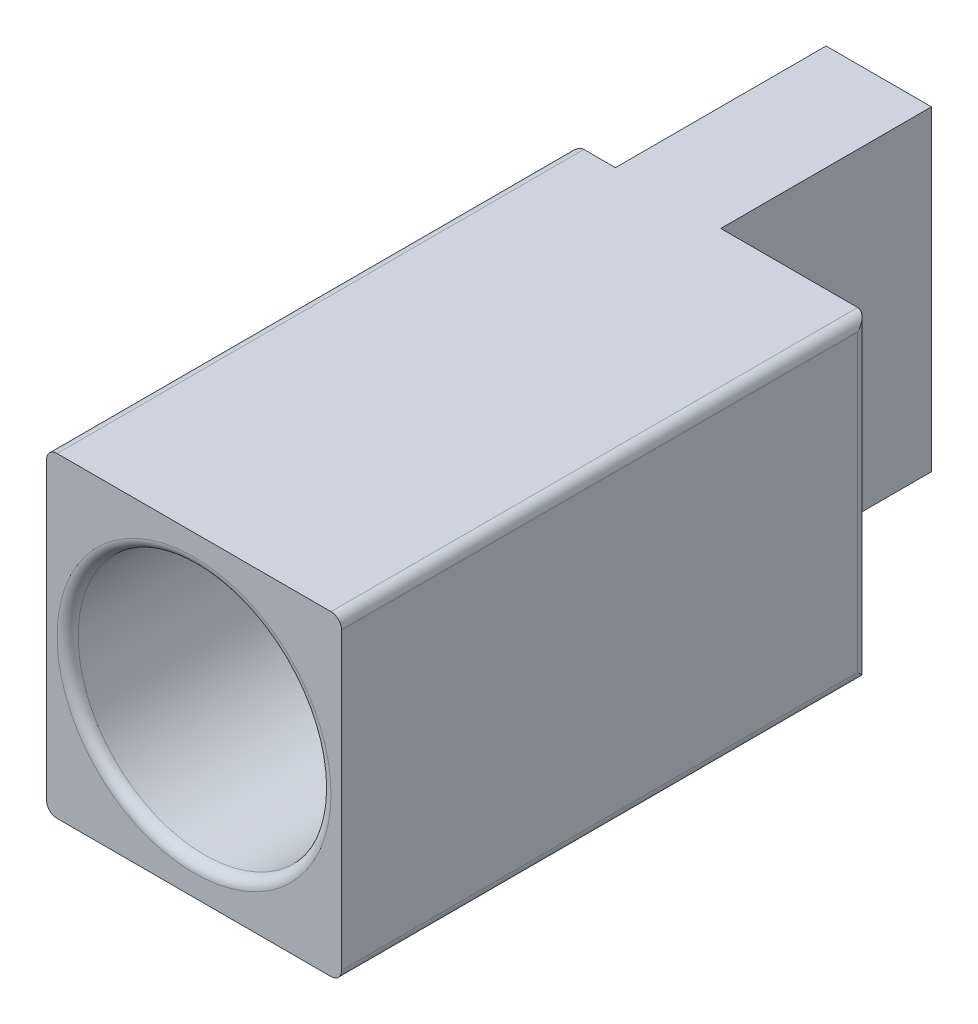
SolidWorks part; units mm, degrees
ref_plane "前视基准面" through (0, 0, 0) normal (0, 0, 1) x (1, 0, 0)
ref_plane "上视基准面" through (0, 0, 0) normal (0, 1, 0) x (1, 0, 0)
ref_plane "右视基准面" through (0, 0, 0) normal (1, 0, 0) x (0, 0, -1)
other "Configuration Table"
sketch "草图1" plane through (0, 0, 0) normal (0, 0, 1) x (1, 0, 0)
  line L1 (0, 0) -> (14, 0)
  line L2 (0, 0) -> (0, -15)
  line L3 (0, -15) -> (14, -15)
  line L4 (14, 0) -> (14, -15)
  line L5 (0, 0) -> (14, -15) construction
  line L6 (0, -15) -> (14, 0) construction
  point P4 (7, -7.5)
  dimension "D1" = 15
  dimension "D2" = 14
extrude "凸台-拉伸1" add sketch "草图1" along normal blind 35
sketch "草图2" plane through (0, 0, 35) normal (0, 0, 1) x (1, 0, 0)
  line L0 (0, 0) -> (14, -15) construction
  circle A0 centre (7, -7.5) radius 6
extrude "切除-拉伸1" cut sketch "草图2" against normal blind 15
sketch "草图3" plane through (0, -15, 0) normal (0, -1, 0) x (1, 0, 0)
  line L0 (0, 0) -> (2, 0) construction
  line L1 (0, 10) -> (2, 10)
  line L3 (7, 0) -> (7, 10)
  line L5 (2, 0) -> (2, 10)
  line L6 (7, 0) -> (14, 0) construction
  line L8 (0, 35) -> (0, 0) construction
  line L9 (14, 35) -> (14, 0) construction
  line L10 (7, 10) -> (14, 10)
  line L11 (2, 0) -> (0, 0)
  line L12 (2, 0) -> (2, 10)
  line L13 (2, 10) -> (0, 10)
  line L14 (0, 0) -> (0, 10)
  line L15 (2, 0) -> (0, 10) construction
  line L16 (2, 10) -> (0, 0) construction
  line L17 (7, 0) -> (14, 0)
  line L18 (7, 0) -> (7, 10)
  line L19 (7, 10) -> (14, 10)
  line L20 (14, 0) -> (14, 10)
  line L21 (7, 0) -> (14, 10) construction
  line L22 (7, 10) -> (14, 0) construction
  point P8 (4.5, 5)
  point P15 (0, 0)
  point P16 (1, 5)
  point P17 (10.5, 5)
  line M5 (0, 0) -> (14, 0)
  line M6 (14, 0) -> (14, 35)
  line M8 (0, 35) -> (0, 0)
  dimension "D1" = 10
extrude "切除-拉伸2" cut sketch "草图3" against normal up to next contours L5 L1 M5 M8 | L10 L3 M5 M6
sketch "草图4" plane through (2, 0, 0) normal (-1, 0, 0) x (0, 0, 1)
  line L0 (0, 0) -> (10, -15) construction
  circle A0 centre (5, -7.5) radius 4
  dimension "D1" = 8
hole_wizard "M4 螺纹孔1" positions "草图5" profile "草图6" tap size "M4" standard "ISO" end condition up to next
sketch "草图5" plane through (2, 0, 0) normal (-1, 0, 0) x (0, 0, 1)
  line L0 (0, 0) -> (10, -15) construction
  point P0 (5, -7.5)
sketch "草图6" plane through (2, -7.5, 5) normal (0, 1, 0) x (0, 0, 1)
  line L0 (0, 0) -> (0, 5)
  line L1 (0, 5) -> (1.65, 5)
  line L2 (1.65, 5) -> (1.65, 0)
  line L5 (1.65, 0) -> (0, 0)
  line L11 (0, -6.35) -> (0, 107.95) construction
  dimension "通孔螺纹孔钻头直径" = 3.3
  dimension "通孔螺纹孔钻头深度" = 5
extrude "切除-拉伸3" cut sketch "草图4" against normal blind 1
fillet "圆角1" radius 0.5 8 edges at (0, 0, 22.5) (14, 0, 22.5) (14, -15, 22.5) (0, -15, 22.5) (13, -7.5, 20) (13, -7.5, 35) (14, -7.5, 10) (0, -7.5, 10)
